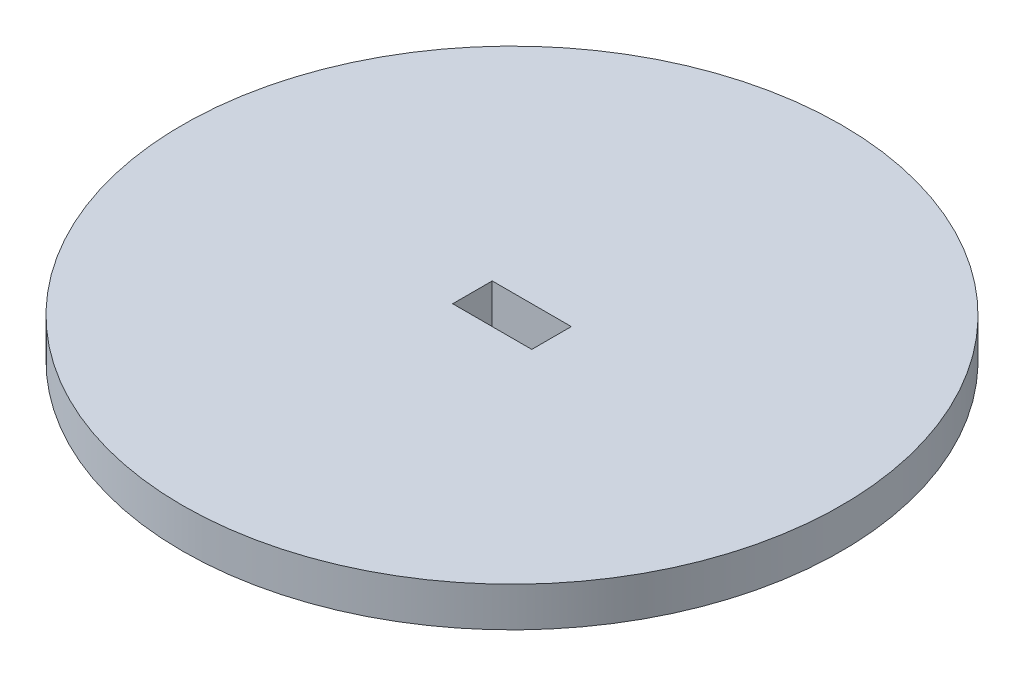
SolidWorks part; units mm, degrees
ref_plane "前视基准面" through (0, 0, 0) normal (0, 0, 1) x (1, 0, 0)
ref_plane "上视基准面" through (0, 0, 0) normal (0, 1, 0) x (1, 0, 0)
ref_plane "右视基准面" through (0, 0, 0) normal (1, 0, 0) x (0, 0, -1)
sketch "草图1" plane through (0, 0, 0) normal (0, 1, 0) x (1, 0, 0)
  circle A0 centre (0, 0) radius 25
  dimension "D1" = 50
extrude "凸台-拉伸1" add sketch "草图1" along normal blind 3
sketch "草图2" plane through (0, 3, 0) normal (0, 1, 0) x (1, 0, 0)
  line L1 (-3, -1.5) -> (3, -1.5)
  line L2 (-3, -1.5) -> (-3, 1.5)
  line L3 (-3, 1.5) -> (3, 1.5)
  line L4 (3, -1.5) -> (3, 1.5)
  line L5 (-3, -1.5) -> (3, 1.5) construction
  line L6 (-3, 1.5) -> (3, -1.5) construction
  point P0 (0, 0)
  dimension "D1" = 6
  dimension "D2" = 3
ref_point "点1"
extrude "切除-拉伸2" cut sketch "草图2" against normal blind 11
